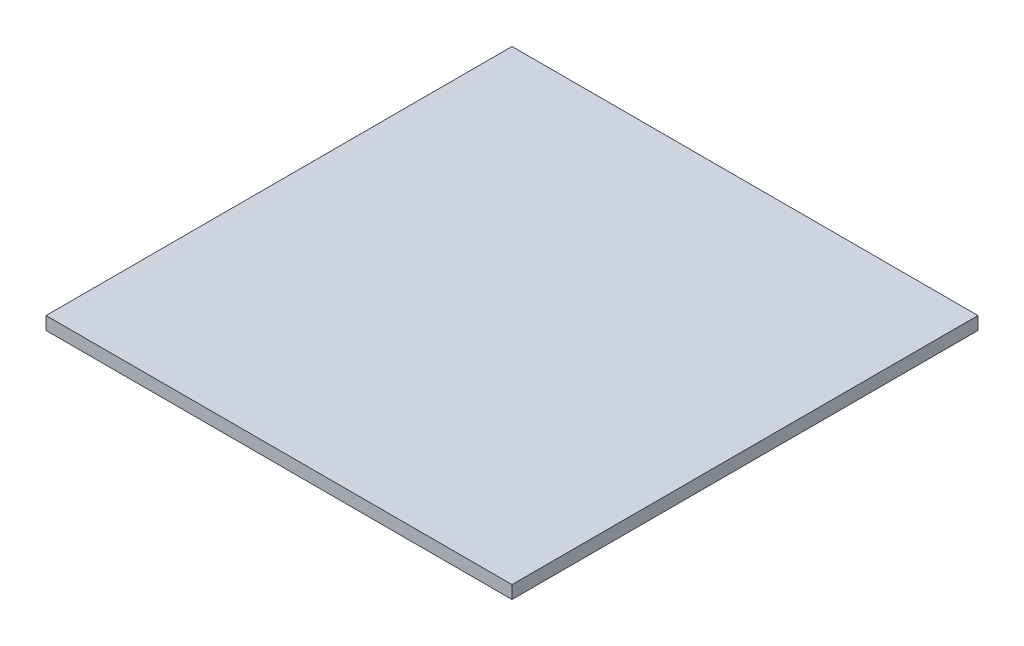
SolidWorks part; units mm, degrees
ref_plane "Спереди" through (0, 0, 0) normal (0, 0, 1) x (1, 0, 0)
ref_plane "Сверху" through (0, 0, 0) normal (0, 1, 0) x (1, 0, 0)
ref_plane "Справа" through (0, 0, 0) normal (1, 0, 0) x (0, 0, -1)
sketch "Эскиз1" plane through (0, 0, 0) normal (0, 1, 0) x (1, 0, 0)
  line L1 (-180, 180) -> (180, 180)
  line L2 (-180, 180) -> (-180, -180)
  line L3 (-180, -180) -> (180, -180)
  line L4 (180, 180) -> (180, -180)
  line L5 (-180, 180) -> (180, -180) construction
  line L6 (-180, -180) -> (180, 180) construction
  point P0 (0, 0)
extrude "Бобышка-Вытянуть1" add sketch "Эскиз1" along normal blind 10
